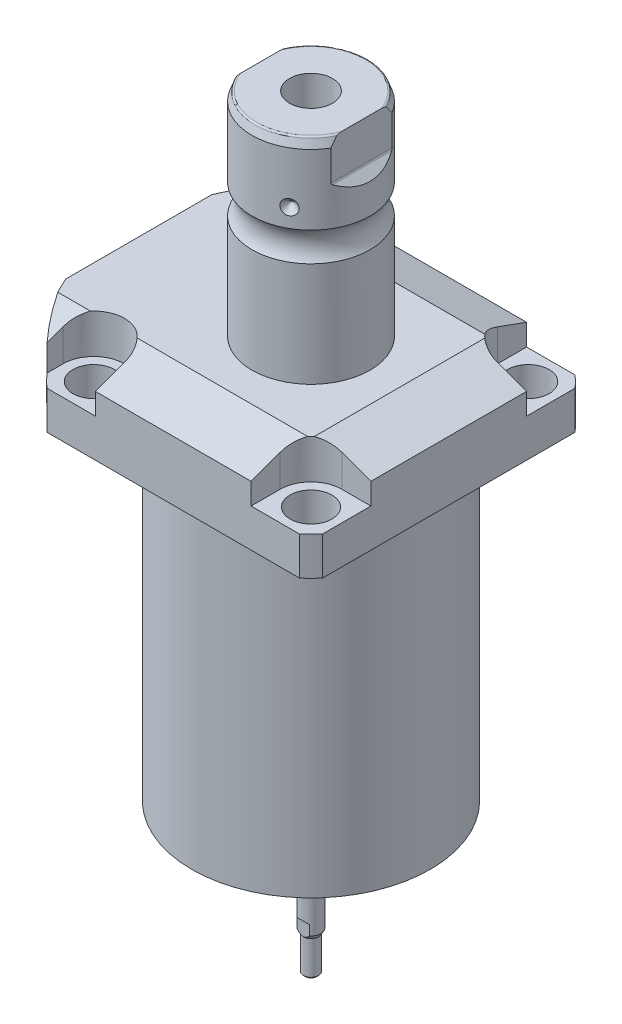
SolidWorks part; units mm, degrees
material "Alloy Steel"
ref_plane "Front Plane" through (0, 0, 0) normal (0, 0, 1) x (1, 0, 0)
ref_plane "Top Plane" through (0, 0, 0) normal (0, 1, 0) x (1, 0, 0)
ref_plane "Right Plane" through (0, 0, 0) normal (1, 0, 0) x (0, 0, -1)
ref_plane "Plane1" through (0, 0, 0) normal (0, 1, 0) x (0, 0, 1)
sketch "Sketch1" plane through (0, 0, 0) normal (0, 1, 0) x (0, 0, 1)
  line L0 (-44.45, 44.45) -> (44.45, 44.45)
  line L1 (44.45, 44.45) -> (44.45, -55.5498)
  line L2 (44.45, -55.5498) -> (-44.45, -55.5498)
  line L3 (-44.45, -55.5498) -> (-44.45, 44.45)
  line L4 (0, 0) -> (0, -60.6467) construction
  dimension "D1" = 55.5498
  dimension "D2" = 99.9998
  dimension "D3" = 88.9
extrude "Extrude1" add sketch "Sketch1" along normal blind 129.794
sketch "Sketch2" plane through (0, 0, 0) normal (0, -1, 0) x (1, 0, 0)
  circle A0 centre (0, 0) radius 60.325
  dimension "D1" = 120.65
extrude "Cut-Extrude1" cut sketch "Sketch2" against normal through all flip side to cut
ref_plane "Plane2" through (0, 0, 0) normal (1, 0, 0) x (0, 0, 1)
sketch "Sketch3" plane through (0, 0, 0) normal (1, 0, 0) x (0, 0, 1)
  line L0 (38.4937, 0) -> (38.4937, -104.775)
  line L1 (38.4937, -104.775) -> (76.5937, -104.775)
  line L2 (76.5937, -104.775) -> (76.5937, 0)
  line L3 (76.5937, 0) -> (38.4937, 0)
  line L4 (0, -93.345) -> (0, 4.445) construction
  line L5 (40.7836, 0) -> (-40.7836, 0) construction
  dimension "D1" = 76.9874
  dimension "D2" = 153.1874
  dimension "D3" = 104.775
revolve "Cut-Revolve1" cut sketch "Sketch3" angle 360 about L4
fillet "Fillet1" radius 0.381 1 edges at (0, 104.775, 38.4937)
sketch "Sketch4" plane through (0, 129.794, 0) normal (0, 1, 0) x (-1, 0, 0)
  line L0 (-44.45, 40.7836) -> (-44.45, -40.7836) construction
  line L1 (40.7836, 44.45) -> (-40.7836, 44.45) construction
  line L2 (-25.1206, -44.45) -> (-25.1206, -35.052)
  line L3 (-44.45, -44.45) -> (-25.1206, -44.45)
  line L4 (-44.45, -25.1206) -> (-44.45, -44.45)
  line L5 (-35.052, -25.1206) -> (-44.45, -25.1206)
  line L6 (44.9834, -44.45) -> (25.1206, -44.45)
  line L7 (25.1206, 44.45) -> (25.1206, 35.052)
  line L8 (44.9834, 44.45) -> (44.9834, 35.052)
  line L9 (44.9834, 44.45) -> (25.1206, 44.45)
  line L10 (-35.052, 25.1206) -> (-44.45, 25.1206)
  line L11 (-44.45, 25.1206) -> (-44.45, 44.45)
  line L12 (-44.45, 44.45) -> (-25.1206, 44.45)
  line L13 (-25.1206, 44.45) -> (-25.1206, 35.052)
  line L14 (-48.9217, 0) -> (49.4551, 0) construction
  line L15 (44.9834, -44.45) -> (44.9834, -35.052)
  line L16 (25.1206, -44.45) -> (25.1206, -35.052)
  arc A0 (25.1206, -35.052) -> (44.9834, -35.052) centre (35.052, -35.052) cw
  arc A1 (-35.052, -25.1206) -> (-25.1206, -35.052) centre (-35.052, -35.052) cw
  arc A2 (-35.052, 25.1206) -> (-25.1206, 35.052) centre (-35.052, 35.052) ccw
  arc A3 (25.1206, 35.052) -> (44.9834, 35.052) centre (35.052, 35.052) ccw
  dimension "D2" = 9.9314
  dimension "D1" = 35.052
  dimension "D3" = 35.052
  dimension "D4" = 35.052
extrude "Cut-Extrude2" cut sketch "Sketch4" against normal blind 12.7
ref_plane "Plane3" through (0, 0, 0) normal (1, 0, 0) x (0, 0, -1)
sketch "Sketch5" plane through (0, 0, 0) normal (1, 0, 0) x (0, 0, -1)
  line L0 (-28.575, 129.794) -> (-44.45, 124.016)
  line L1 (0, 0) -> (0, 154.1081) construction
  line L2 (-28.575, 129.794) -> (-44.45, 129.794)
  line L3 (-44.45, 129.794) -> (-44.45, 124.016)
  dimension "D1" = 15.875
  dimension "D2" = 20
extrude "Cut-Extrude9" cut sketch "Sketch5" against normal through all and the other way through all
mirror "Mirror1" about plane through (0, 0, 0) normal (0, 0, 1) of "Cut-Extrude9"
ref_plane "Plane7" through (0, 0, 0) normal (0, 0, 1) x (1, 0, 0)
sketch "Sketch9" plane through (0, 0, 0) normal (0, 0, 1) x (1, 0, 0)
  line L0 (28.575, 129.794) -> (44.45, 124.016)
  line L1 (44.45, 124.016) -> (44.45, 129.794)
  line L2 (44.45, 129.794) -> (28.575, 129.794)
  dimension "D1" = 15.875
  dimension "D2" = 20
extrude "Cut-Extrude7" cut sketch "Sketch9" against normal through all and the other way through all
ref_plane "Plane8" through (-41.402, 88.9, -18.1102) normal (1, 0, 0) x (0, 1, 0)
sketch "Sketch20" plane through (-41.402, 88.9, -18.1102) normal (1, 0, 0) x (0, 1, 0)
  line L0 (-88.9, 18.1102) -> (39.8401, 18.1102) construction
  line L1 (-7.2797, 36.2204) -> (36.9042, 36.2204) construction
  line L2 (15.875, 41.9227) -> (17.3228, 41.9227)
  line L3 (15.875, 58.8938) -> (15.875, -22.6734) construction
  line L4 (17.3228, 41.9227) -> (17.3228, 39.4716)
  line L5 (17.3228, 39.4716) -> (18.3388, 39.4716)
  line L6 (18.3388, 39.4716) -> (18.3388, 37.465)
  line L7 (18.3388, 37.465) -> (29.3116, 37.465)
  line L8 (29.3116, 37.465) -> (29.3116, 36.2204)
  line L9 (29.3116, 36.2204) -> (15.875, 36.2204)
  line L10 (15.875, 41.9227) -> (15.875, 36.2204)
  dimension "D1" = 18.1102
  dimension "D2" = 11.4046
  dimension "D3" = 1.4478
  dimension "D4" = 6.5024
  dimension "D5" = 1.016
  dimension "D6" = 2.4892
  dimension "D7" = 10.9728
revolve "Cut-Revolve4" cut sketch "Sketch20" angle 360 about L1
mirror "Mirror10" about plane through (0, 0, 0) normal (0, 0, 1) of "Cut-Revolve4"
sketch "Sketch10" plane through (-41.402, 88.9, -18.1102) normal (1, 0, 0) x (0, 1, 0)
  line L0 (-1.0325, 0) -> (1.5659, 0) construction
  line L1 (29.3116, 1.2446) -> (18.3388, 1.2446) construction
  line L2 (18.3388, -1.2446) -> (29.3116, -1.2446) construction
  line L3 (15.875, 58.8938) -> (15.875, -22.6734) construction
  circle A0 centre (16.1417, 4.5212) radius 1.1811
  dimension "D1" = 2.3622
  dimension "D2" = 0.2667
  dimension "D3" = 9.0424
revolve "Revolve4" add sketch "Sketch10" angle 360 about L0
ref_plane "Plane9" through (-41.402, 88.9, 18.1102) normal (1, 0, 0) x (0, 1, 0)
sketch "Sketch11" plane through (-41.402, 88.9, 18.1102) normal (1, 0, 0) x (0, 1, 0)
  line L0 (-1.0325, 0) -> (1.5659, 0) construction
  line L1 (29.3116, 1.2446) -> (18.3388, 1.2446) construction
  line L3 (15.875, 22.6734) -> (15.875, -58.8938) construction
  line L4 (18.3388, -1.2446) -> (29.3116, -1.2446) construction
  circle A0 centre (16.1417, 4.5212) radius 1.1811
  point P10 (0, 0)
  dimension "D1" = 2.3622
  dimension "D2" = 9.0424
  dimension "D3" = 0.2667
revolve "Revolve2" add sketch "Sketch11" angle 360 about L0
ref_plane "Plane10" through (-55.5498, 101.9048, 12.9794) normal (0, 0, 1) x (0, 1, 0)
sketch "S2D0007" plane through (-55.5498, 101.9048, 12.9794) normal (0, 0, 1) x (0, 1, 0)
  line L0 (15.875, 0) -> (26.3525, 0)
  line L1 (26.3525, 0) -> (26.3525, -0.254)
  line L2 (26.3525, -0.254) -> (22.0599, -0.254)
  line L3 (22.0599, -0.254) -> (21.5173, -2.8067)
  line L4 (21.5173, -2.8067) -> (20.8534, -3.4706)
  line L5 (20.8534, -3.4706) -> (20.8534, -14.224)
  line L6 (20.8534, -14.224) -> (15.875, -14.224)
  line L7 (15.875, -14.224) -> (15.875, 0)
  line L8 (15.875, -14.9352) -> (15.875, 0.7112) construction
  line L9 (2.8702, 0) -> (2.8702, -14.7662) construction
  line L10 (27.8892, 0) -> (2.8702, 0) construction
  dimension "D1" = 0.254
  dimension "D2" = 13.0048
  dimension "D3" = 12
  dimension "D4" = 0.254
  dimension "D5" = 20.955
  dimension "D6" = 12.3698
  dimension "D7" = 45
  dimension "D8" = 3.2166
  dimension "D9" = 9.9568
  dimension "D10" = 13.97
revolve "Cut-Revolve2" cut sketch "S2D0007" angle 360 about L8
pattern_linear "LPattern1" count 2 spacing 25.9588 along (0, 0, -1) of "Cut-Revolve2"
ref_plane "Plane12" through (0, 0, 0) normal (1, 0, 0) x (0, -1, 0)
sketch "Sketch15" plane through (0, 0, 0) normal (1, 0, 0) x (0, -1, 0)
  line L0 (-129.794, 0) -> (-129.794, 19.05)
  line L1 (-129.794, 19.05) -> (-163.4663, 19.05)
  line L2 (-172.8805, 19.05) -> (-195.4276, 19.05)
  line L3 (-198.3486, 17.9868) -> (-198.3486, 0)
  line L4 (-198.3486, 0) -> (-129.794, 0)
  line L5 (-197.6361, 0) -> (-64.6704, 0) construction
  line L6 (-129.794, 27.5233) -> (-129.794, -27.5233) construction
  line L7 (-104.775, 40.7836) -> (-104.775, 44.45) construction
  line L8 (-198.3486, 17.9868) -> (-195.4276, 19.05)
  arc A0 (-172.8805, 19.05) -> (-163.4663, 19.05) centre (-168.1734, 25.4254) ccw
  dimension "D2" = 20
  dimension "D4" = 7.9248
  dimension "D6" = 35.0012
  dimension "D1" = 93.5736
  dimension "D3" = 38.1
  dimension "D5" = 30.1752
  dimension "D7" = 2.921
revolve "Revolve3" add sketch "Sketch15" angle 360 about L5
ref_plane "Plane13" through (0, 0, 0) normal (0, 0, -1) x (0, -1, 0)
sketch "Sketch16" plane through (0, 0, 0) normal (0, 0, -1) x (0, -1, 0)
  line L0 (-198.3486, 19.05) -> (-182.5644, 19.05)
  line L1 (-198.3486, -19.05) -> (-198.3486, -16.2814)
  line L2 (-198.3486, 16.2814) -> (-185.6486, 16.2814)
  line L3 (-185.1098, 16.5046) -> (-182.5644, 19.05)
  line L4 (-185.1098, -16.5046) -> (-182.5644, -19.05)
  line L5 (-198.3486, -16.2814) -> (-185.6486, -16.2814)
  line L6 (-198.3486, 19.05) -> (-198.3486, 16.2814)
  line L7 (-198.3486, -19.05) -> (-182.5644, -19.05)
  line L8 (-194.0458, 0) -> (-125.0021, 0) construction
  line L11 (-198.3486, 17.9868) -> (-198.3486, -17.9868) construction
  line L12 (-172.8805, 19.05) -> (-195.4276, 19.05) construction
  arc A0 (-185.6486, 16.2814) -> (-185.1098, 16.5046) centre (-185.6486, 17.0434) ccw
  arc A1 (-185.6486, -16.2814) -> (-185.1098, -16.5046) centre (-185.6486, -17.0434) cw
  point P3 (-185.333, 16.2814)
  dimension "D4" = 0.762
  dimension "D1" = 32.5628
  dimension "D2" = 45
  dimension "D3" = 12.7
extrude "Cut-Extrude8" cut sketch "Sketch16" against normal mid plane 106.68
hole_wizard "Hole1" positions "Sketch18" profile "Sketch17" legacy end condition up to next
sketch "Sketch18" plane through (0, 117.094, 0) normal (0, 1, 0) x (-1, 0, 0)
  arc A0 (44.9834, -35.052) -> (25.1206, -35.052) centre (35.052, -35.052) ccw construction
  arc A1 (25.1206, 35.052) -> (44.9834, 35.052) centre (35.052, 35.052) ccw construction
  arc A2 (-35.052, 25.1206) -> (-25.1206, 35.052) centre (-35.052, 35.052) ccw construction
  arc A3 (-25.1206, -35.052) -> (-35.052, -25.1206) centre (-35.052, -35.052) ccw construction
  point P0 (-35.052, -35.052)
  point P1 (-35.052, 35.052)
  point P3 (35.052, 35.052)
  point P5 (35.052, -35.052)
sketch "Sketch17" plane through (35.052, 117.094, -35.052) normal (1, 0, 0) x (0, 0, 1)
  line L0 (0, 0) -> (0, 12.319)
  line L1 (0, 12.319) -> (6.7437, 12.319)
  line L2 (6.7437, 12.319) -> (6.7437, 0)
  line L3 (6.7437, 0) -> (0, 0)
  line L4 (0, 110) -> (0, -10) construction
  dimension "Diameter" = 13.4874
  dimension "Depth" = 12.319
chamfer "Chamfer1" distance 0.635 angle 45 2 edges at (-41.402, 107.2388, 16.8656) (-41.402, 107.2388, -16.8656)
sketch "Sketch21" plane through (0, 0, 0) normal (0, 0, 1) x (1, 0, 0)
  line L0 (0, 0) -> (0, 194.0957) construction
  line L1 (0, 172.9486) -> (6.9342, 177.1151)
  line L2 (6.9342, 177.1151) -> (6.9342, 198.3486)
  line L4 (6.9342, 198.3486) -> (0, 198.3486)
  line L5 (0, 198.3486) -> (0, 172.9486)
  line L6 (16.2814, 198.3486) -> (-16.2814, 198.3486) construction
  dimension "D1" = 13.8684
  dimension "D2" = 59
  dimension "D3" = 25.4
revolve "Cut-Revolve5" cut sketch "Sketch21" angle 360 about L0
fillet "Fillet2" radius 0.635 2 edges at (0, 198.3486, 17.9868) (0, 198.3486, -17.9868)
sketch "Sketch22" plane through (0, 0, 0) normal (0, 0, 1) x (1, 0, 0)
  line L0 (-37.9974, 178.8414) -> (37.12, 178.8414) construction
  line L1 (-19.05, 181.2544) -> (-16.637, 178.8414)
  line L2 (-16.637, 178.8414) -> (-19.05, 178.8414)
  line L3 (-19.05, 178.8414) -> (-19.05, 181.2544)
  line L4 (-19.05, 182.5644) -> (-19.05, 172.8805) construction
  arc A0 (-19.05, 163.4663) -> (-19.05, 172.8805) centre (-25.4254, 168.1734) ccw construction
  dimension "D2" = 10.668
  dimension "D1" = 4.826
  dimension "D3" = 45
revolve "Cut-Revolve6" cut sketch "Sketch22" angle 360 about L0
pattern_circular "CirPattern1" count 3 over 360 about axis through (0, 197.6361, 0) along (0, 1, 0) of "Cut-Revolve6"
sketch "Sketch23" plane through (0, 0, 0) normal (1, 0, 0) x (0, 0, -1)
  line L0 (0, -1000) -> (0, 49000) construction
  line L1 (0, 0) -> (3.175, 0)
  line L2 (-38.4937, 0) -> (38.4937, 0) construction
  line L3 (3.175, 0) -> (3.175, -35.605)
  line L4 (3.175, -35.605) -> (2.4384, -36.8808)
  line L5 (2.4384, -36.8808) -> (2.4384, -47.6758)
  line L6 (2.4384, -47.6758) -> (1.8034, -48.3108)
  line L7 (1.8034, -48.3108) -> (0, -48.3108)
  line L8 (0, -48.3108) -> (0, 0)
  line L9 (17.5422, 198.3486) -> (6.5303, 198.3486) construction
  dimension "D1" = 246.6594
  dimension "D2" = 45
  dimension "D3" = 4.8768
  dimension "D4" = 6.35
  dimension "D5" = 30
  dimension "D6" = 11.43
  dimension "D7" = 0.635
revolve "Revolve5" add sketch "Sketch23" angle 360 about L0
sketch "Sketch24" plane through (0, 0, 0) normal (1, 0, 0) x (0, 0, -1)
  line L0 (0, -1000) -> (0, 49000) construction
  line L1 (3.175, -31.7627) -> (2.5019, -32.4358)
  line L2 (3.175, -35.605) -> (3.175, 0) construction
  line L3 (2.5019, -32.4358) -> (2.5019, -48.3108)
  line L4 (-1.8034, -48.3108) -> (1.8034, -48.3108) construction
  line L5 (3.175, -31.7627) -> (3.175, -48.3108)
  line L6 (3.175, -48.3108) -> (2.5019, -48.3108)
  line L7 (-3.175, -48.3108) -> (-2.5019, -48.3108)
  line L8 (-2.5019, -32.4358) -> (-2.5019, -48.3108)
  line L9 (-3.175, -31.7627) -> (-2.5019, -32.4358)
  line L10 (-3.175, -31.7627) -> (-3.175, -48.3108)
  dimension "D1" = 45
  dimension "D2" = 15.875
  dimension "D3" = 5.0038
extrude "Cut-Extrude10" cut sketch "Sketch24" against normal mid plane 7.62
sketch "Sketch25" plane through (0, 0, 0) normal (1, 0, 0) x (0, 0, -1)
  line L0 (0, -1000) -> (0, 49000) construction
  line L1 (-38.4937, 0) -> (38.4937, 0) construction
  line L2 (11.6459, 0) -> (14.351, 0)
  line L3 (11.6459, 0) -> (11.6459, 1.3208)
  line L4 (11.6459, 1.3208) -> (14.351, 1.3208)
  line L5 (14.351, 0) -> (14.351, 1.3208)
  dimension "D1" = 23.2918
  dimension "D2" = 28.702
  dimension "D3" = 1.3208
revolve "Cut-Revolve7" cut sketch "Sketch25" angle 360 about L0
sketch "Sketch26" plane through (0, 0, 0) normal (0, -1, 0) x (1, 0, 0)
  line L0 (0, -1000) -> (0, 49000) construction
  line L1 (-1000, 0) -> (49000, 0) construction
  line L2 (0, 0) -> (48296.2913, -12940.9523) construction
  line L3 (0, 0) -> (25000, 43301.2702) construction
  circle A0 centre (0, 0) radius 19.431 construction
  circle A1 centre (19.431, 0) radius 1.27
  circle A2 centre (18.7689, -5.0291) radius 1.27
  circle A3 centre (-9.7155, 16.8277) radius 1.27
  circle A4 centre (-13.7398, 13.7398) radius 1.27
  circle A5 centre (-13.7398, -13.7398) radius 1.27
  circle A6 centre (-9.7155, -16.8277) radius 1.27
  dimension "D3" = 38.862
  dimension "D4" = 2.54
  dimension "D5" = 2.54
  dimension "D1" = 15
  dimension "D2" = 60
extrude "Cut-Extrude11" cut sketch "Sketch26" against normal blind 7.62
